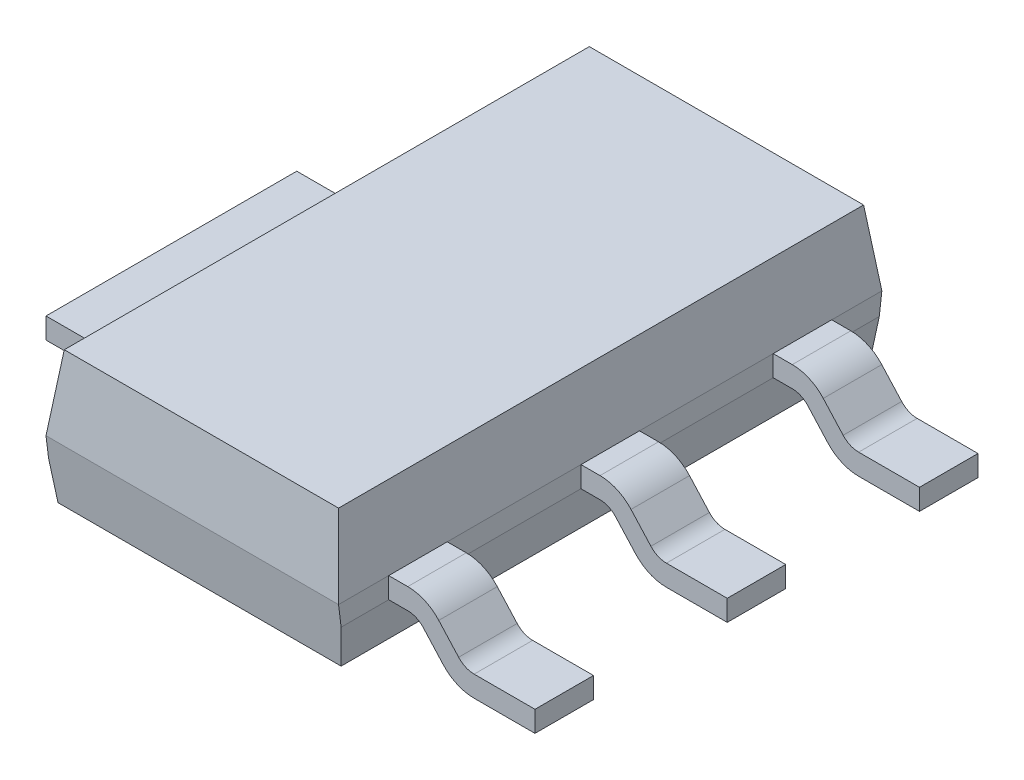
SolidWorks part; units mm, degrees
ref_plane "Front Plane" through (0, 0, 0) normal (0, 0, 1) x (1, 0, 0)
ref_plane "Top Plane" through (0, 0, 0) normal (0, 1, 0) x (1, 0, 0)
ref_plane "Right Plane" through (0, 0, 0) normal (1, 0, 0) x (0, 0, -1)
sketch "Sketch1" plane through (0, 0, 0) normal (0, 0, 1) x (1, 0, 0)
  line L0 (0, -2.055) -> (0, 2.0542) construction
  line L1 (-6.4969, 0) -> (9.4954, 0) construction
  line L2 (-1.6407, 0.89) -> (1.6407, 0.89)
  line L3 (-1.75, -0.25) -> (-1.6935, -0.71)
  line L4 (-1.75, 0) -> (-1.6407, 0.89)
  line L5 (1.6935, -0.71) -> (-1.6935, -0.71)
  line L8 (3.5, -0.51) -> (3.5, -0.76)
  line L9 (3.5, -0.76) -> (2.772, -0.76)
  line L10 (-2.0627, -0.76) -> (4.0802, -0.76) construction
  line L11 (3.5, -0.51) -> (2.772, -0.51)
  line L12 (1.75, 0) -> (1.978, 0)
  line L13 (1.75, -0.25) -> (1.978, -0.25)
  line L14 (2.1634, -0.3324) -> (2.4011, -0.5953)
  line L15 (2.5866, -0.4276) -> (2.3489, -0.1647)
  line L16 (-2.5866, -0.4276) -> (-2.3489, -0.1647)
  line L17 (-2.1634, -0.3324) -> (-2.4011, -0.5953)
  line L18 (-1.75, -0.25) -> (-1.978, -0.25)
  line L19 (-1.75, 0) -> (-1.978, 0)
  line L20 (-3.5, -0.51) -> (-2.772, -0.51)
  line L21 (-3.5, -0.76) -> (-2.772, -0.76)
  line L22 (-3.5, -0.51) -> (-3.5, -0.76)
  line L23 (1.75, 0) -> (1.6407, 0.89)
  line L24 (1.75, -0.25) -> (1.6935, -0.71)
  arc A0 (2.772, -0.51) -> (2.5866, -0.4276) centre (2.772, -0.26) cw
  arc A1 (1.978, -0.25) -> (2.1634, -0.3324) centre (1.978, -0.5) cw
  arc A2 (1.978, 0) -> (2.3489, -0.1647) centre (1.978, -0.5) cw
  arc A3 (2.772, -0.76) -> (2.4011, -0.5953) centre (2.772, -0.26) cw
  arc A4 (-2.772, -0.76) -> (-2.4011, -0.5953) centre (-2.772, -0.26) ccw
  arc A5 (-1.978, 0) -> (-2.3489, -0.1647) centre (-1.978, -0.5) ccw
  arc A6 (-1.978, -0.25) -> (-2.1634, -0.3324) centre (-1.978, -0.5) ccw
  arc A7 (-2.772, -0.51) -> (-2.5866, -0.4276) centre (-2.772, -0.26) ccw
  point P27 (2.2, 0)
  point P30 (2.55, -0.76)
  point P42 (-2.55, -0.76)
  point P43 (-2.2, 0)
  dimension "D11" = 0.45
  dimension "D3" = 0.25
  dimension "D4" = 7
  dimension "D1" = 1.6
  dimension "D2" = 3.5
  dimension "D5" = 0.25
  dimension "D6" = 7
  dimension "D7" = 0.05
  dimension "D8" = 0.89
  dimension "D9" = 7
  dimension "D10" = 1.978
extrude "Extrude1" add sketch "Sketch1" along normal mid plane 6.5
sketch "Sketch2" plane through (0, 0.89, 0) normal (0, 1, 0) x (1, 0, 0)
  line L1 (-3.5, 3.25) -> (-1.75, 3.25)
  line L2 (-3.5, 3.25) -> (-3.5, 1.5)
  line L3 (-3.5, 1.5) -> (-1.75, 1.5)
  line L4 (-1.75, 3.25) -> (-1.75, 1.5)
  line L5 (-1.8321, 0) -> (1.6779, 0) construction
  line L6 (0, -1.6706) -> (0, 1.8101) construction
  line L7 (-1.75, -3.25) -> (-1.75, -1.5)
  line L8 (-3.5, -3.25) -> (-1.75, -3.25)
  line L9 (-3.5, -3.25) -> (-3.5, -1.5)
  line L10 (-3.5, -1.5) -> (-1.75, -1.5)
  line L12 (1.75, 0.35) -> (3.5, 0.35)
  line L14 (1.75, -0.35) -> (3.5, -0.35)
  line L15 (1.75, -3.25) -> (1.75, 3.25) construction
  line L17 (-3.5, -3.25) -> (-3.5, 3.25) construction
  line L18 (1.75, 2.65) -> (3.5, 2.65)
  line L19 (1.75, 0.35) -> (1.75, 1.95)
  line L20 (1.75, 1.95) -> (3.5, 1.95)
  line L21 (3.5, 2.65) -> (3.5, 1.95) construction
  line L23 (3.5, 1.95) -> (3.5, 0.35)
  line L24 (1.75, -2.65) -> (3.5, -2.65)
  line L25 (3.5, -2.65) -> (3.5, -1.95) construction
  line L26 (1.75, -1.95) -> (3.5, -1.95)
  line L27 (-2.772, 3.25) -> (-3.5, 3.25) construction
  line L32 (-1.75, -3.25) -> (-1.75, 3.25) construction
  line L33 (1.75, -0.35) -> (1.75, -1.95)
  line L34 (1.75, -2.65) -> (1.75, -3.25)
  line L35 (1.75, -3.25) -> (3.5, -3.25)
  line L36 (3.5, -3.25) -> (3.5, -2.65)
  line L37 (3.5, 2.65) -> (3.5, 3.25)
  line L38 (3.5, 3.25) -> (1.75, 3.25)
  line L39 (1.75, 3.25) -> (1.75, 2.65)
  line L40 (3.5, -0.35) -> (3.5, -1.95)
  point P30 (3.5, 2.3)
  point P31 (3.5, -2.3)
  dimension "D1" = 3
  dimension "D2" = 0.7
  dimension "D3" = 0.7
  dimension "D4" = 4.6
extrude "Cut-Extrude1" cut sketch "Sketch2" against normal through all
sketch "Sketch3" plane through (0, 0, 0) normal (1, 0, 0) x (0, 0, -1)
  line L0 (3.1407, 0.89) -> (3.25, 0)
  line L1 (3.1407, 0.89) -> (3.25, 0.89)
  line L3 (-1.5689, 0) -> (1.5803, 0) construction
  line L4 (0, -0.9098) -> (0, 0.7925) construction
  line L11 (3.25, 0) -> (3.25, 0.89)
  line L13 (-3.25, 0) -> (-3.25, 0.89)
  line L14 (-3.1407, 0.89) -> (-3.25, 0.89)
  line L15 (-3.1407, 0.89) -> (-3.25, 0)
  line L16 (3.25, 0) -> (3.25, 0.89) construction
  line L17 (-3.25, 0.89) -> (3.25, 0.89) construction
  line L18 (2.65, 0) -> (3.25, 0) construction
  dimension "D1" = 7
extrude "Cut-Extrude3" cut sketch "Sketch3" against normal mid plane 3.5
sketch "Sketch4" plane through (0, 0, 0) normal (1, 0, 0) x (0, 0, -1)
  line L0 (3.1628, -0.71) -> (3.25, -0.71)
  line L1 (3.25, -0.71) -> (3.25, 0)
  line L2 (3.25, 0) -> (3.1628, -0.71)
  line L3 (0, -0.7055) -> (0, 0.8436) construction
  line L4 (-3.25, -0.71) -> (3.25, -0.71) construction
  line L7 (-3.25, 0) -> (-3.1628, -0.71)
  line L8 (-3.25, -0.71) -> (-3.25, 0)
  line L9 (-3.1628, -0.71) -> (-3.25, -0.71)
  dimension "D1" = 7
extrude "Cut-Extrude4" cut sketch "Sketch4" against normal mid plane 3.5
